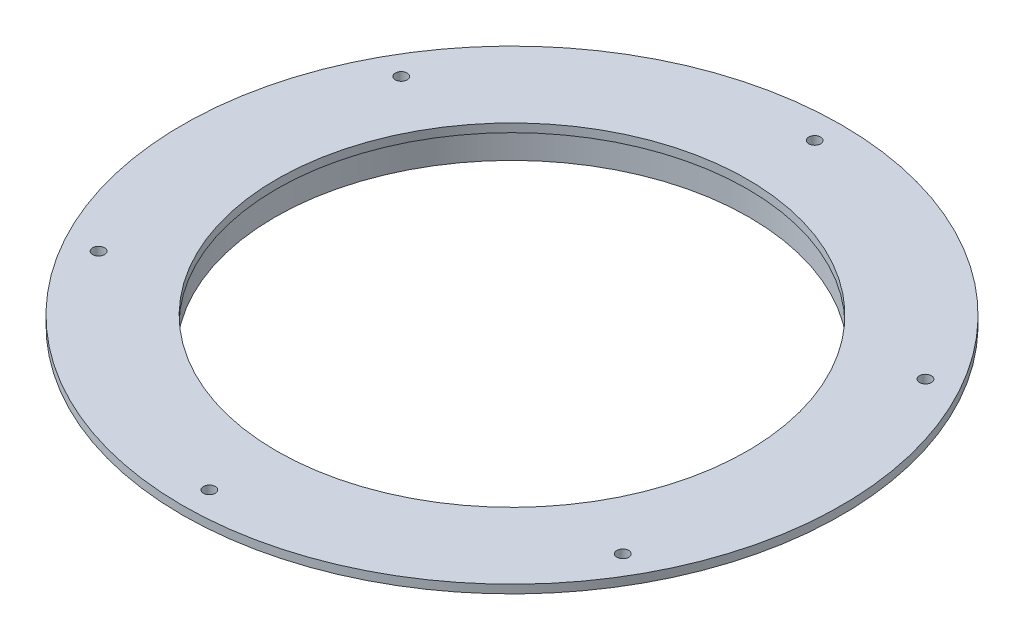
SolidWorks part; units mm, degrees
material "PVC Rigid"
ref_plane "Front Plane" through (0, 0, 0) normal (0, 0, 1) x (1, 0, 0)
ref_plane "Top Plane" through (0, 0, 0) normal (0, 1, 0) x (1, 0, 0)
ref_plane "Right Plane" through (0, 0, 0) normal (1, 0, 0) x (0, 0, -1)
sketch "Sketch1" plane through (0, 0, 0) normal (1, 0, 0) x (0, 0, -1)
  line L0 (89.535, 0) -> (92.71, 0)
  line L1 (92.71, 0) -> (92.71, 9.525)
  line L2 (92.71, 9.525) -> (124.46, 9.525)
  line L3 (124.46, 9.525) -> (124.46, 12.7)
  line L4 (124.46, 12.7) -> (0, 12.7)
  line L5 (0, 12.7) -> (0, 9.525)
  line L6 (0, 9.525) -> (89.535, 9.525)
  line L7 (89.535, 9.525) -> (89.535, 0)
  line L8 (0, 0) -> (0, 12.7) construction
  dimension "D1" = 12.7
  dimension "D2" = 3.175
  dimension "D3" = 92.71
  dimension "D4" = 124.46
  dimension "D5" = 3.175
  dimension "D6" = 12.7
revolve "Revolve1" add sketch "Sketch1" angle 360 about L8
hole_wizard "#8 Clearance Hole1" positions "Sketch2" profile "Sketch3" hole size "#8" standard "ANSI Inch" end condition up to next
sketch "Sketch2" plane through (0, 12.7, 0) normal (0, 1, 0) x (1, 0, 0)
  line L1 (0, 114.3) -> (-98.9867, 57.15)
  line L2 (-98.9867, 57.15) -> (-98.9867, -57.15)
  line L3 (-98.9867, -57.15) -> (0, -114.3)
  line L4 (0, -114.3) -> (98.9867, -57.15)
  line L5 (98.9867, -57.15) -> (98.9867, 57.15)
  line L6 (98.9867, 57.15) -> (0, 114.3)
  circle A1 centre (0, 0) radius 98.9867 construction
  point P0 (0, 114.3)
  dimension "D1" = 114.3
sketch "Sketch3" plane through (0, 12.7, -114.3) normal (1, 0, 0) x (0, 0, 1)
  line L0 (0, 0) -> (0, 3.176)
  line L1 (0, 3.176) -> (2.2479, 3.176)
  line L2 (2.2479, 3.176) -> (2.2479, 0)
  line L5 (2.2479, 0) -> (0, 0)
  line L11 (0, -6.35) -> (0, 107.95) construction
  dimension "Thru Hole Dia." = 4.4958
  dimension "Thru Hole Depth" = 3.176
pattern_circular "CirPattern1" count 6 over 360 about axis through (0, 0, 0) along (0, 1, 0) of "#8 Clearance Hole1"
sketch "Sketch4" plane through (0, 12.7, 0) normal (0, 1, 0) x (1, 0, 0)
  circle A0 centre (0, 0) radius 88.9
  dimension "D1" = 177.8
extrude "Cut-Extrude1" cut sketch "Sketch4" against normal through all
